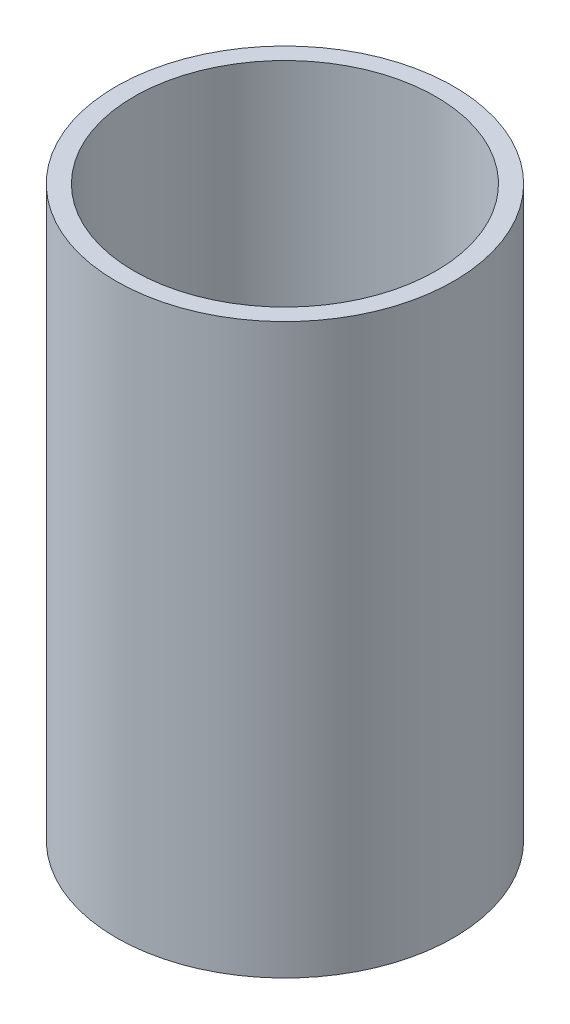
SolidWorks part; units mm, degrees
ref_plane "Front Plane" through (0, 0, 0) normal (0, 0, 1) x (1, 0, 0)
ref_plane "Top Plane" through (0, 0, 0) normal (0, 1, 0) x (1, 0, 0)
ref_plane "Right Plane" through (0, 0, 0) normal (1, 0, 0) x (0, 0, -1)
sketch "Sketch1" plane through (0, 0, 0) normal (0, 1, 0) x (1, 0, 0)
  circle A0 centre (0, 0) radius 30.1625
  circle A1 centre (0, 0) radius 26.9875
extrude "Boss-Extrude1" add sketch "Sketch1" along normal blind 101.6
